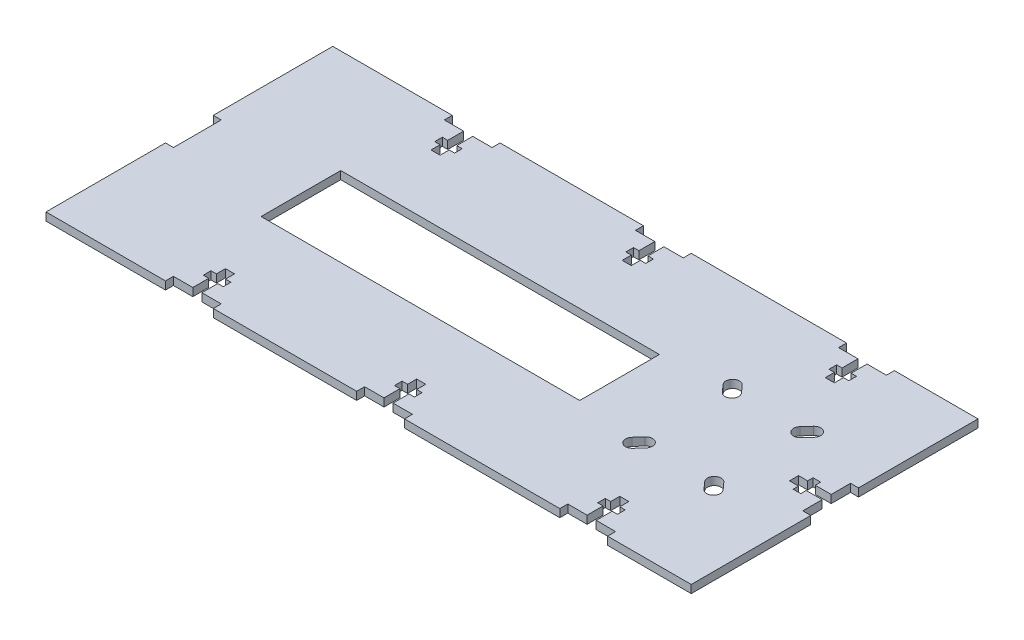
SolidWorks part; units mm, degrees
ref_plane "Front Plane" through (0, 0, 0) normal (0, 0, 1) x (1, 0, 0)
ref_plane "Top Plane" through (0, 0, 0) normal (0, 1, 0) x (1, 0, 0)
ref_plane "Right Plane" through (0, 0, 0) normal (1, 0, 0) x (0, 0, -1)
sketch "Sketch2" plane through (0, 0, 0) normal (0, 1, 0) x (1, 0, 0)
  line L0 (-102.87, -45.72) -> (-64.77, -45.72)
  line L1 (-102.87, 45.72) -> (102.87, 45.72) construction
  line L2 (-102.87, 45.72) -> (-102.87, -45.72) construction
  line L3 (-102.87, -45.72) -> (102.87, -45.72) construction
  line L4 (102.87, 45.72) -> (102.87, -45.72) construction
  line L5 (-102.87, 45.72) -> (102.87, -45.72) construction
  line L6 (-102.87, -45.72) -> (102.87, 45.72) construction
  line L7 (-64.77, -45.72) -> (-64.77, -43.18)
  line L9 (-49.53, -43.18) -> (-49.53, -45.72)
  line L10 (-49.53, -45.72) -> (-3.81, -45.72)
  line L11 (-3.81, -45.72) -> (-3.81, -43.18)
  line L12 (-3.81, -43.18) -> (11.43, -43.18) construction
  line L13 (11.43, -43.18) -> (11.43, -45.72)
  line L14 (11.43, -45.72) -> (60.96, -45.72)
  line L15 (60.96, -45.72) -> (60.96, -43.18)
  line L16 (60.96, -43.18) -> (76.2, -43.18) construction
  line L17 (76.2, -43.18) -> (76.2, -45.72)
  line L18 (76.2, -45.72) -> (102.87, -45.72)
  line L21 (-102.87, 0) -> (102.87, 0) construction
  line L22 (76.2, 43.18) -> (76.2, 45.72)
  line L23 (60.96, 43.18) -> (76.2, 43.18) construction
  line L24 (60.96, 45.72) -> (60.96, 43.18)
  line L25 (11.43, 43.18) -> (11.43, 45.72)
  line L26 (-3.81, 43.18) -> (11.43, 43.18) construction
  line L27 (-3.81, 45.72) -> (-3.81, 43.18)
  line L28 (-49.53, 43.18) -> (-49.53, 45.72)
  line L29 (-64.77, 43.18) -> (-49.53, 43.18) construction
  line L30 (-64.77, 45.72) -> (-64.77, 43.18)
  line L31 (-102.87, 45.72) -> (-64.77, 45.72)
  line L32 (-49.53, 45.72) -> (-3.81, 45.72)
  line L33 (11.43, 45.72) -> (60.96, 45.72)
  line L34 (76.2, 45.72) -> (102.87, 45.72)
  line L35 (-102.87, 45.72) -> (-102.87, 7.62)
  line L36 (-102.87, 7.62) -> (-100.33, 7.62)
  line L37 (-100.33, 7.62) -> (-100.33, -7.62)
  line L38 (-100.33, -7.62) -> (-102.87, -7.62)
  line L39 (-102.87, -7.62) -> (-102.87, -45.72)
  line L40 (0, 45.72) -> (0, -45.72) construction
  line L41 (100.33, -7.62) -> (102.87, -7.62)
  line L42 (102.87, 7.62) -> (100.33, 7.62)
  line L43 (100.33, 7.62) -> (100.33, -7.62) construction
  line L44 (102.87, 45.72) -> (102.87, 7.62)
  line L45 (102.87, -7.62) -> (102.87, -45.72)
  line L46 (-58.5978, -43.18) -> (-58.5978, -38.1)
  line L47 (-58.5978, -38.1) -> (-60.325, -38.1)
  line L48 (-60.325, -38.1) -> (-60.325, -35.668)
  line L49 (-60.325, -35.668) -> (-58.5978, -35.668)
  line L50 (-58.5978, -35.668) -> (-58.5978, -32.766)
  line L51 (-58.5978, -32.766) -> (-55.7022, -32.766)
  line L52 (-64.77, -43.18) -> (-58.5978, -43.18)
  line L53 (-49.53, -43.18) -> (-55.7022, -43.18)
  line L54 (-55.7022, -43.18) -> (-55.7022, -38.1)
  line L55 (-55.7022, -38.1) -> (-53.975, -38.1)
  line L56 (-53.975, -38.1) -> (-53.975, -35.668)
  line L57 (-64.77, -43.18) -> (-49.53, -43.18) construction
  line L58 (-57.15, -43.18) -> (-57.15, -32.766) construction
  line L59 (-53.975, -35.668) -> (-55.7022, -35.668)
  line L60 (-55.7022, -35.668) -> (-55.7022, -32.766)
  line L61 (-3.81, -43.18) -> (2.3622, -43.18)
  line L62 (2.3622, -43.18) -> (2.3622, -38.1)
  line L63 (2.3622, -38.1) -> (0.635, -38.1)
  line L64 (0.635, -38.1) -> (0.635, -35.6679)
  line L65 (0.635, -35.6679) -> (2.3622, -35.6679)
  line L66 (2.3622, -35.6679) -> (2.3622, -32.766)
  line L67 (2.3622, -32.766) -> (5.2578, -32.766)
  line L68 (3.81, -43.18) -> (3.81, -32.766) construction
  line L69 (11.43, -43.18) -> (5.2578, -43.18)
  line L70 (5.2578, -43.18) -> (5.2578, -38.1)
  line L71 (5.2578, -38.1) -> (6.985, -38.1)
  line L72 (6.985, -38.1) -> (6.985, -35.6679)
  line L73 (6.985, -35.6679) -> (5.2578, -35.6679)
  line L74 (5.2578, -35.6679) -> (5.2578, -32.766)
  line L75 (68.58, -43.18) -> (68.58, -32.766) construction
  line L76 (60.96, -43.18) -> (67.1322, -43.18)
  line L77 (67.1322, -43.18) -> (67.1322, -38.1)
  line L78 (67.1322, -38.1) -> (65.405, -38.1)
  line L79 (65.405, -38.1) -> (65.405, -35.6679)
  line L80 (65.405, -35.6679) -> (67.1322, -35.6679)
  line L81 (67.1322, -35.6679) -> (67.1322, -32.766)
  line L82 (67.1322, -32.766) -> (70.0278, -32.766)
  line L83 (70.0278, -35.6679) -> (70.0278, -32.766)
  line L84 (71.755, -35.6679) -> (70.0278, -35.6679)
  line L85 (71.755, -38.1) -> (71.755, -35.6679)
  line L86 (70.0278, -38.1) -> (71.755, -38.1)
  line L87 (76.2, -43.18) -> (70.0278, -43.18)
  line L88 (70.0278, -43.18) -> (70.0278, -38.1)
  line L89 (76.2, 43.18) -> (70.0278, 43.18)
  line L90 (70.0278, 43.18) -> (70.0278, 38.1)
  line L91 (70.0278, 38.1) -> (71.755, 38.1)
  line L92 (71.755, 38.1) -> (71.755, 35.6679)
  line L93 (71.755, 35.6679) -> (70.0278, 35.6679)
  line L94 (70.0278, 35.6679) -> (70.0278, 32.766)
  line L95 (67.1322, 32.766) -> (70.0278, 32.766)
  line L96 (67.1322, 35.6679) -> (67.1322, 32.766)
  line L97 (65.405, 35.6679) -> (67.1322, 35.6679)
  line L98 (65.405, 38.1) -> (65.405, 35.6679)
  line L99 (67.1322, 38.1) -> (65.405, 38.1)
  line L100 (67.1322, 43.18) -> (67.1322, 38.1)
  line L101 (60.96, 43.18) -> (67.1322, 43.18)
  line L102 (11.43, 43.18) -> (5.2578, 43.18)
  line L103 (5.2578, 43.18) -> (5.2578, 38.1)
  line L104 (5.2578, 38.1) -> (6.985, 38.1)
  line L105 (6.985, 38.1) -> (6.985, 35.6679)
  line L106 (6.985, 35.6679) -> (5.2578, 35.6679)
  line L107 (5.2578, 35.6679) -> (5.2578, 32.766)
  line L108 (2.3622, 32.766) -> (5.2578, 32.766)
  line L109 (0.635, 35.6679) -> (2.3622, 35.6679)
  line L110 (2.3622, 38.1) -> (0.635, 38.1)
  line L111 (0.635, 38.1) -> (0.635, 35.6679)
  line L112 (2.3622, 43.18) -> (2.3622, 38.1)
  line L113 (-3.81, 43.18) -> (2.3622, 43.18)
  line L114 (-49.53, 43.18) -> (-55.7022, 43.18)
  line L115 (-55.7022, 43.18) -> (-55.7022, 38.1)
  line L116 (-55.7022, 38.1) -> (-53.975, 38.1)
  line L117 (-53.975, 38.1) -> (-53.975, 35.6679)
  line L118 (-53.975, 35.6679) -> (-55.7022, 35.6679)
  line L119 (-55.7022, 35.6679) -> (-55.7022, 32.766)
  line L120 (-58.5978, 32.766) -> (-55.7022, 32.766)
  line L121 (-58.5978, 35.6679) -> (-58.5978, 32.766)
  line L122 (-60.325, 35.6679) -> (-58.5978, 35.6679)
  line L123 (-60.325, 38.1) -> (-60.325, 35.6679)
  line L124 (-58.5978, 38.1) -> (-60.325, 38.1)
  line L125 (-58.5978, 43.18) -> (-58.5978, 38.1)
  line L126 (-64.77, 43.18) -> (-58.5978, 43.18)
  line L127 (2.3622, 35.6679) -> (2.3622, 32.766)
  line L128 (100.33, -1.4478) -> (95.25, -1.4478)
  line L129 (95.25, -1.4478) -> (95.25, -3.175)
  line L130 (95.25, -3.175) -> (92.8179, -3.175)
  line L131 (92.8179, -3.175) -> (92.8179, -1.4478)
  line L132 (92.8179, -1.4478) -> (89.916, -1.4478)
  line L133 (89.916, -1.4478) -> (89.916, 1.4478)
  line L134 (100.33, -1.4478) -> (100.33, -7.62)
  line L135 (92.8179, 1.4478) -> (89.916, 1.4478)
  line L136 (92.8179, 3.175) -> (92.8179, 1.4478)
  line L137 (95.25, 3.175) -> (92.8179, 3.175)
  line L138 (95.25, 1.4478) -> (95.25, 3.175)
  line L139 (100.33, 1.4478) -> (95.25, 1.4478)
  line L140 (100.33, 1.4478) -> (100.33, 7.62)
  point P0 (0, 0)
  point P128 (89.916, 0)
  dimension "D1" = 205.74
  dimension "D2" = 91.44
  dimension "D3" = 38.1
  dimension "D4" = 15.24
  dimension "D5" = 2.54
  dimension "D6" = 45.72
  dimension "D7" = 49.53
  dimension "D8" = 15.24
  dimension "D9" = 2.54
  dimension "D10" = 12.954
  dimension "D11" = 5.08
  dimension "D12" = 2.432
  dimension "D13" = 6.35
  dimension "D14" = 2.8956
  dimension "D15" = 12.954
  dimension "D16" = 5.08
  dimension "D17" = 2.432
  dimension "D18" = 6.35
  dimension "D19" = 2.8956
  dimension "D20" = 12.954
  dimension "D21" = 5.08
  dimension "D22" = 2.432
  dimension "D23" = 6.35
  dimension "D24" = 2.8956
  dimension "D25" = 12.954
  dimension "D26" = 2.432
  dimension "D27" = 5.08
  dimension "D28" = 2.8956
  dimension "D29" = 6.35
extrude "Boss-Extrude1" add sketch "Sketch2" against normal blind 2.54
sketch "Sketch3" plane through (0, 0, 0) normal (0, 1, 0) x (1, 0, 0)
  line L0 (0, 0) -> (67.31, 0) construction
  line L1 (51.308, 19.05) -> (83.312, 19.05) construction
  line L2 (51.308, 19.05) -> (51.308, -19.05) construction
  line L3 (51.308, -19.05) -> (83.312, -19.05) construction
  line L4 (83.312, 19.05) -> (83.312, -19.05) construction
  line L5 (51.308, 19.05) -> (83.312, -19.05) construction
  line L6 (51.308, -19.05) -> (83.312, 19.05) construction
  line L7 (80.264, 16.002) -> (78.232, 13.7302) construction
  line L8 (81.8732, 14.5627) -> (79.8412, 12.2908)
  line L9 (78.6548, 17.4413) -> (76.6228, 15.1695)
  line L10 (67.31, 0) -> (67.31, 19.05) construction
  line L11 (54.356, 16.002) -> (56.388, 13.7302) construction
  line L12 (52.7468, 14.5627) -> (54.7788, 12.2908)
  line L13 (55.9652, 17.4413) -> (57.9972, 15.1695)
  line L14 (80.264, -16.002) -> (78.232, -13.7302) construction
  line L15 (81.8732, -14.5627) -> (79.8412, -12.2908)
  line L16 (78.6548, -17.4413) -> (76.6228, -15.1695)
  line L17 (54.356, -16.002) -> (56.388, -13.7302) construction
  line L18 (52.7468, -14.5627) -> (54.7788, -12.2908)
  line L19 (55.9652, -17.4413) -> (57.9972, -15.1695)
  arc A0 (81.8732, 14.5627) -> (78.6548, 17.4413) centre (80.264, 16.002) ccw
  arc A1 (76.6228, 15.1695) -> (79.8412, 12.2908) centre (78.232, 13.7302) ccw
  arc A2 (52.7468, 14.5627) -> (55.9652, 17.4413) centre (54.356, 16.002) cw
  arc A3 (57.9972, 15.1695) -> (54.7788, 12.2908) centre (56.388, 13.7302) cw
  arc A4 (81.8732, -14.5627) -> (78.6548, -17.4413) centre (80.264, -16.002) cw
  arc A5 (76.6228, -15.1695) -> (79.8412, -12.2908) centre (78.232, -13.7302) cw
  arc A6 (52.7468, -14.5627) -> (55.9652, -17.4413) centre (54.356, -16.002) ccw
  arc A7 (57.9972, -15.1695) -> (54.7788, -12.2908) centre (56.388, -13.7302) ccw
  point P0 (67.31, 0)
  point P8 (79.248, 14.8661)
  point P26 (55.372, 14.8661)
  point P33 (79.248, -14.8661)
  point P40 (55.372, -14.8661)
  dimension "D4" = 2.159
  dimension "D8" = 5.08
  dimension "D1" = 38.1
  dimension "D2" = 32.004
  dimension "D3" = 67.31
  dimension "D5" = 3.048
  dimension "D6" = 3.048
  dimension "D7" = 3.048
extrude "Cut-Extrude1" cut sketch "Sketch3" against normal up to next
sketch "Sketch4" plane through (0, 0, 0) normal (0, 1, 0) x (1, 0, 0)
  line L0 (102.87, 7.62) -> (102.87, 45.72) construction
  line L1 (-67.31, 12.7) -> (34.29, 12.7)
  line L2 (-67.31, 12.7) -> (-67.31, -12.7)
  line L3 (-67.31, -12.7) -> (34.29, -12.7)
  line L4 (34.29, 12.7) -> (34.29, -12.7)
  line L5 (-67.31, 12.7) -> (34.29, -12.7) construction
  line L6 (-67.31, -12.7) -> (34.29, 12.7) construction
  point P0 (-16.51, 0)
  point P5 (0, 0)
  dimension "D1" = 25.4
  dimension "D2" = 101.6
  dimension "D3" = 68.58
extrude "Cut-Extrude2" cut sketch "Sketch4" against normal up to next
